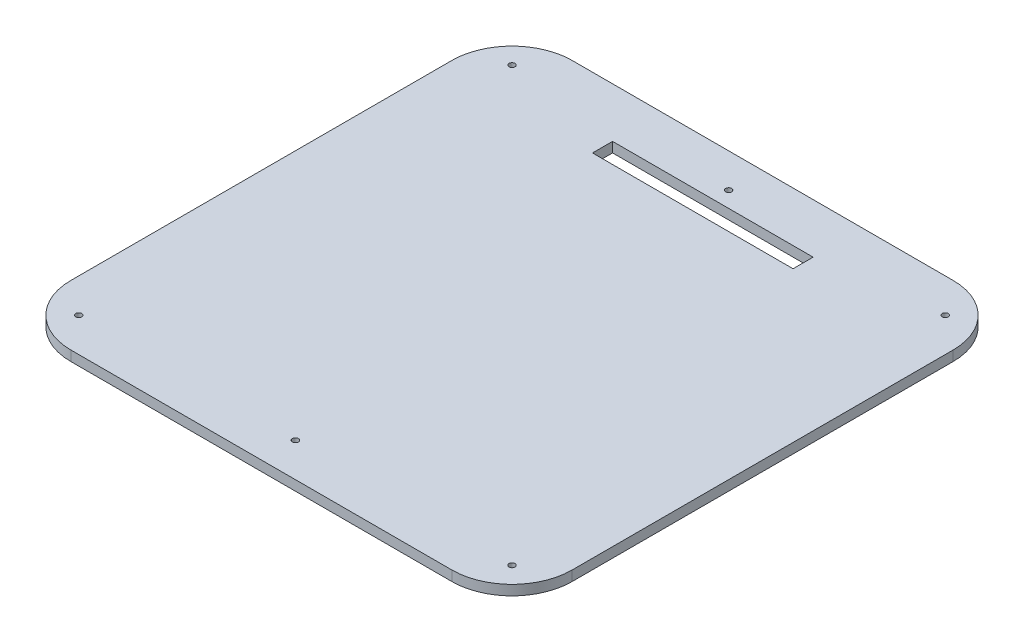
SolidWorks part; units mm, degrees
ref_plane "Front Plane" through (0, 0, 0) normal (0, 0, 1) x (1, 0, 0)
ref_plane "Top Plane" through (0, 0, 0) normal (0, 1, 0) x (1, 0, 0)
ref_plane "Right Plane" through (0, 0, 0) normal (1, 0, 0) x (0, 0, -1)
sketch "Sketch1" plane through (0, 0, 0) normal (0, 1, 0) x (1, 0, 0)
  line L1 (-125, 125) -> (125, 125)
  line L2 (-125, 125) -> (-125, -125)
  line L3 (-125, -125) -> (125, -125)
  line L4 (125, 125) -> (125, -125)
  line L5 (-125, 125) -> (125, -125) construction
  line L6 (-125, -125) -> (125, 125) construction
  point P0 (0, 0)
  dimension "D1" = 250
  dimension "D2" = 250
extrude "Boss-Extrude1" add sketch "Sketch1" along normal mid plane 5
sketch "Sketch2" plane through (0, 2.5, 0) normal (0, 1, 0) x (1, 0, 0)
  line L0 (0, 0) -> (0, 125) construction
  line L1 (-50, 100.1392) -> (50, 100.1392)
  line L2 (-50, 100.1392) -> (-50, 90.1392)
  line L3 (-50, 90.1392) -> (50, 90.1392)
  line L4 (50, 100.1392) -> (50, 90.1392)
  line L5 (-50, 100.1392) -> (50, 90.1392) construction
  line L6 (-50, 90.1392) -> (50, 100.1392) construction
  line L7 (125, 125) -> (-125, 125) construction
  line L8 (0, 125) -> (0, -125) construction
  line L9 (-125, -125) -> (125, -125) construction
  point P0 (0, 95.1392)
  point P5 (50, 95.1392)
  point P11 (0, 0)
  point P15 (0, 95.1392)
  dimension "D1" = 10
  dimension "D2" = 100
extrude "Cut-Extrude1" cut sketch "Sketch2" against normal up to next
sketch "Sketch4" plane through (0, 2.5, 0) normal (0, 1, 0) x (1, 0, 0)
  line L0 (0, 0) -> (0, 125) construction
  line L1 (125, 125) -> (-125, 125) construction
  line L2 (0, 125) -> (0, -125) construction
  line L3 (-125, -125) -> (125, -125) construction
  line L4 (-125, 0) -> (125, 0) construction
  line L5 (-125, 125) -> (-125, -125) construction
  line L6 (125, -125) -> (125, 125) construction
  circle A0 centre (-108, 108) radius 1.5
  circle A1 centre (0, 108) radius 1.5
  circle A2 centre (108, 108) radius 1.5
  circle A3 centre (108, -108) radius 1.5
  circle A4 centre (0, -108) radius 1.5
  circle A5 centre (-108, -108) radius 1.5
  dimension "D2" = 3
  dimension "D3" = 3
extrude "Cut-Extrude2" cut sketch "Sketch4" against normal up to next
fillet "Fillet1" radius 30 4 edges at (-125, 0, 125) (125, 0, 125) (125, 0, -125) (-125, 0, -125)
